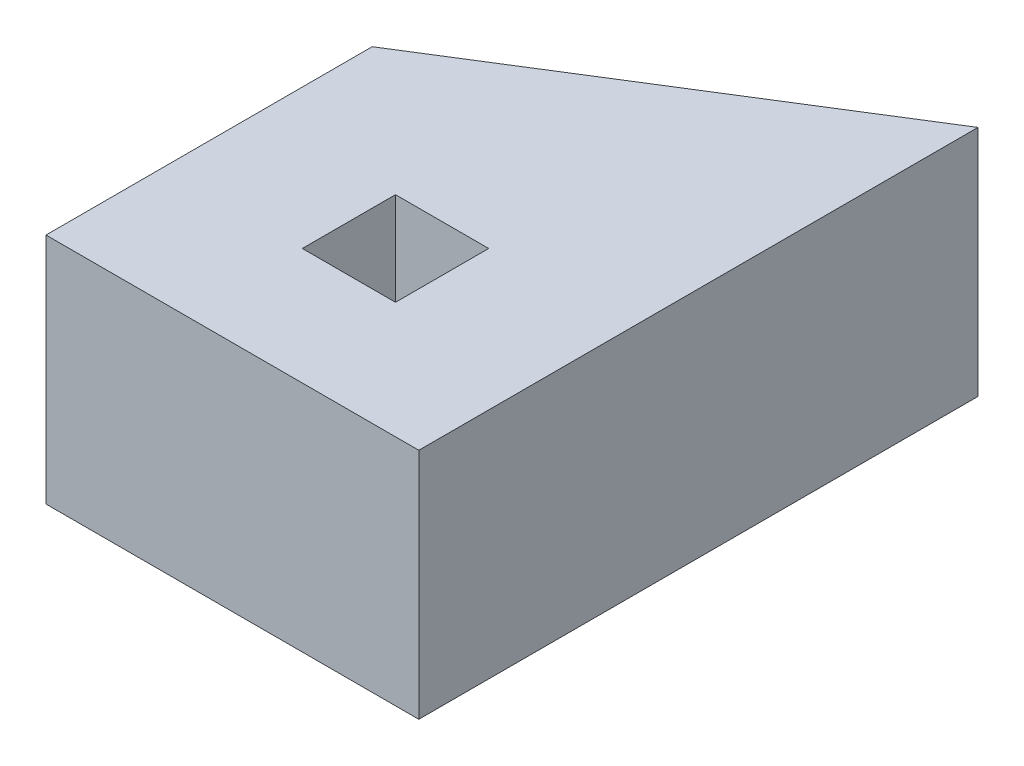
SolidWorks part; units mm, degrees
ref_plane "Front Plane" through (0, 0, 0) normal (0, 0, 1) x (1, 0, 0)
ref_plane "Top Plane" through (0, 0, 0) normal (0, 1, 0) x (1, 0, 0)
ref_plane "Right Plane" through (0, 0, 0) normal (1, 0, 0) x (0, 0, -1)
sketch "Sketch1" plane through (0, 0, 0) normal (0, 1, 0) x (1, 0, 0)
  line L0 (40, 35) -> (40, 85)
  line L1 (-40, -35) -> (40, -35)
  line L2 (-40, -35) -> (-40, 35)
  line L3 (-40, 35) -> (40, 35)
  line L4 (40, -35) -> (40, 35)
  line L5 (-40, -35) -> (40, 35) construction
  line L6 (-40, 35) -> (40, -35) construction
  line L7 (40, 85) -> (-40, 35)
  point P0 (0, 0)
  dimension "D1" = 80
  dimension "D2" = 70
  dimension "H1" = 50
extrude "Boss-Extrude1" add sketch "Sketch1" along normal blind 50 contours L1 L4 L3 L2 | L0 L7 L3
sketch "Sketch2" plane through (0, 50, 0) normal (0, 1, 0) x (1, 0, 0)
  line L1 (-10, -10) -> (10, -10)
  line L2 (-10, -10) -> (-10, 10)
  line L3 (-10, 10) -> (10, 10)
  line L4 (10, -10) -> (10, 10)
  line L5 (-10, -10) -> (10, 10) construction
  line L6 (-10, 10) -> (10, -10) construction
  point P0 (0, 0)
  dimension "Key" = 20
extrude "Cut-Extrude1" cut sketch "Sketch2" against normal through all
